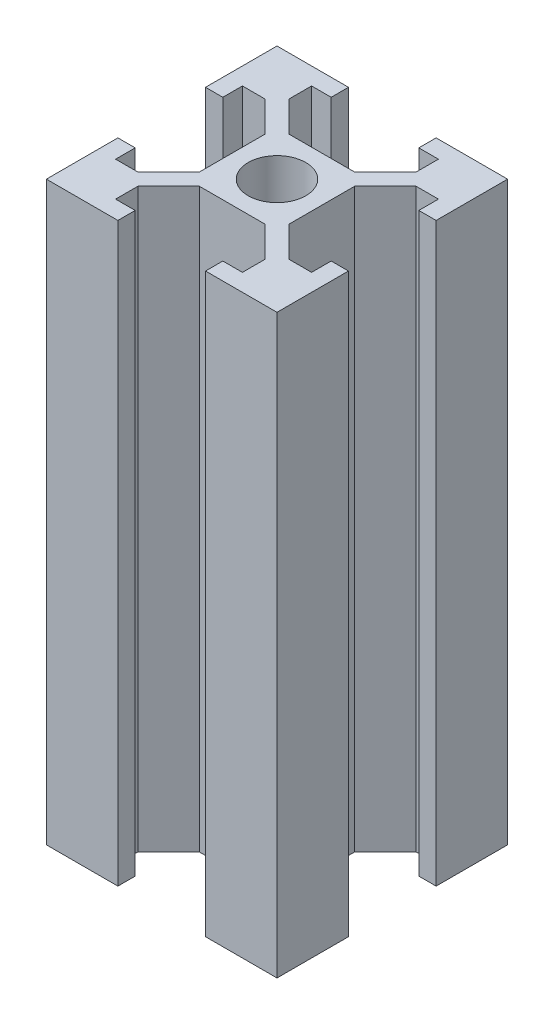
SolidWorks part; units mm, degrees
ref_plane "前视基准面" through (0, 0, 0) normal (0, 0, 1) x (1, 0, 0)
ref_plane "上视基准面" through (0, 0, 0) normal (0, 1, 0) x (1, 0, 0)
ref_plane "右视基准面" through (0, 0, 0) normal (1, 0, 0) x (0, 0, -1)
sketch "草图1" plane through (0, 0, 0) normal (0, 1, 0) x (1, 0, 0)
  line L0 (-6.5607, 5.5) -> (-3.9, 2.8393)
  line L1 (-10, 10) -> (10, 10)
  line L2 (-10, 10) -> (-10, -10)
  line L3 (-10, -10) -> (10, -10)
  line L4 (10, 10) -> (10, -10)
  line L5 (-10, 10) -> (10, -10) construction
  line L6 (-10, -10) -> (10, 10) construction
  line L7 (-3.9, 3.9) -> (3.9, 3.9)
  line L8 (-3.9, 3.9) -> (-3.9, -3.9)
  line L9 (-3.9, -3.9) -> (3.9, -3.9)
  line L10 (3.9, 3.9) -> (3.9, -3.9)
  line L11 (-3.9, 3.9) -> (3.9, -3.9) construction
  line L12 (-3.9, -3.9) -> (3.9, 3.9) construction
  line L13 (-10, 10) -> (-5.5, 10)
  line L14 (-10, 10) -> (-10, 5.5)
  line L15 (-10, 5.5) -> (-5.5, 5.5)
  line L16 (-5.5, 10) -> (-5.5, 5.5)
  line L17 (-10, 5.5) -> (-8.5, 5.5)
  line L18 (-10, 5.5) -> (-10, 3.8)
  line L19 (-10, 3.8) -> (-8.5, 3.8)
  line L20 (-8.5, 5.5) -> (-8.5, 3.8)
  line L21 (-5.5, 6.5607) -> (-2.8393, 3.9)
  line L22 (-3.8, 10) -> (-3.8, 8.5)
  line L23 (-5.5, 8.5) -> (-3.8, 8.5)
  line L24 (0, 10) -> (0, -10) construction
  line L25 (5.5, 8.5) -> (3.8, 8.5)
  line L26 (3.8, 10) -> (3.8, 8.5)
  line L27 (5.5, 6.5607) -> (2.8393, 3.9)
  line L28 (6.5607, 5.5) -> (3.9, 2.8393)
  line L29 (10, 3.8) -> (8.5, 3.8)
  line L30 (8.5, 5.5) -> (8.5, 3.8)
  line L31 (10, 5.5) -> (8.5, 5.5)
  line L32 (10, 5.5) -> (10, 3.8)
  line L33 (10, 5.5) -> (5.5, 5.5)
  line L34 (5.5, 10) -> (5.5, 5.5)
  line L35 (10, 10) -> (5.5, 10)
  line L36 (10, 10) -> (10, 5.5)
  line L37 (-10, 0) -> (10, 0) construction
  line L38 (-10, -3.8) -> (-8.5, -3.8)
  line L39 (-8.5, -5.5) -> (-8.5, -3.8)
  line L40 (-10, -5.5) -> (-5.5, -5.5)
  line L41 (-6.5607, -5.5) -> (-3.9, -2.8393)
  line L42 (-5.5, -6.5607) -> (-2.8393, -3.9)
  line L43 (-5.5, -10) -> (-5.5, -5.5)
  line L44 (-5.5, -8.5) -> (-3.8, -8.5)
  line L45 (-3.8, -10) -> (-3.8, -8.5)
  line L46 (3.8, -10) -> (3.8, -8.5)
  line L47 (6.5607, -5.5) -> (3.9, -2.8393)
  line L48 (5.5, -6.5607) -> (2.8393, -3.9)
  line L49 (-10, 10) -> (10, 10)
  line L50 (-10, -10) -> (10, -10)
  line L51 (5.5, -8.5) -> (3.8, -8.5)
  line L52 (5.5, -10) -> (5.5, -5.5)
  line L53 (10, -5.5) -> (5.5, -5.5)
  line L54 (10, -3.8) -> (8.5, -3.8)
  line L55 (8.5, -5.5) -> (8.5, -3.8)
  circle A0 centre (0, 0) radius 2.5
  dimension "D1" = 5
  dimension "D2" = 20
  dimension "D3" = 20
  dimension "D4" = 7.8
  dimension "D5" = 4.5
  dimension "D6" = 1.7
  dimension "D7" = 0.75
  dimension "D8" = 1.5
extrude "凸台-拉伸1" add sketch "草图1" along normal blind 50 contours L1 L34 L33 L31 L4 | L4 L31 L30 L29 | L34 L27 L7 L10 L28 L33 | L34 L1 L26 L25 | L10 L7 L8 L9 A0 | L16 L23 L22 L1 | L16 L1 L2 L15 | L20 L15 L2 L19 | L21 L16 L15 L0 L8 L7 | L3 L43 L40 L2 | L3 L45 L44 L43 | L2 L40 L39 L38 | L43 L42 L9 L8 L41 L40 | L53 L47 L10 L9 L48 L52 | L4 L53 L52 L50 | L55 L53 L4 L54 | L3 L52 L51 L46
